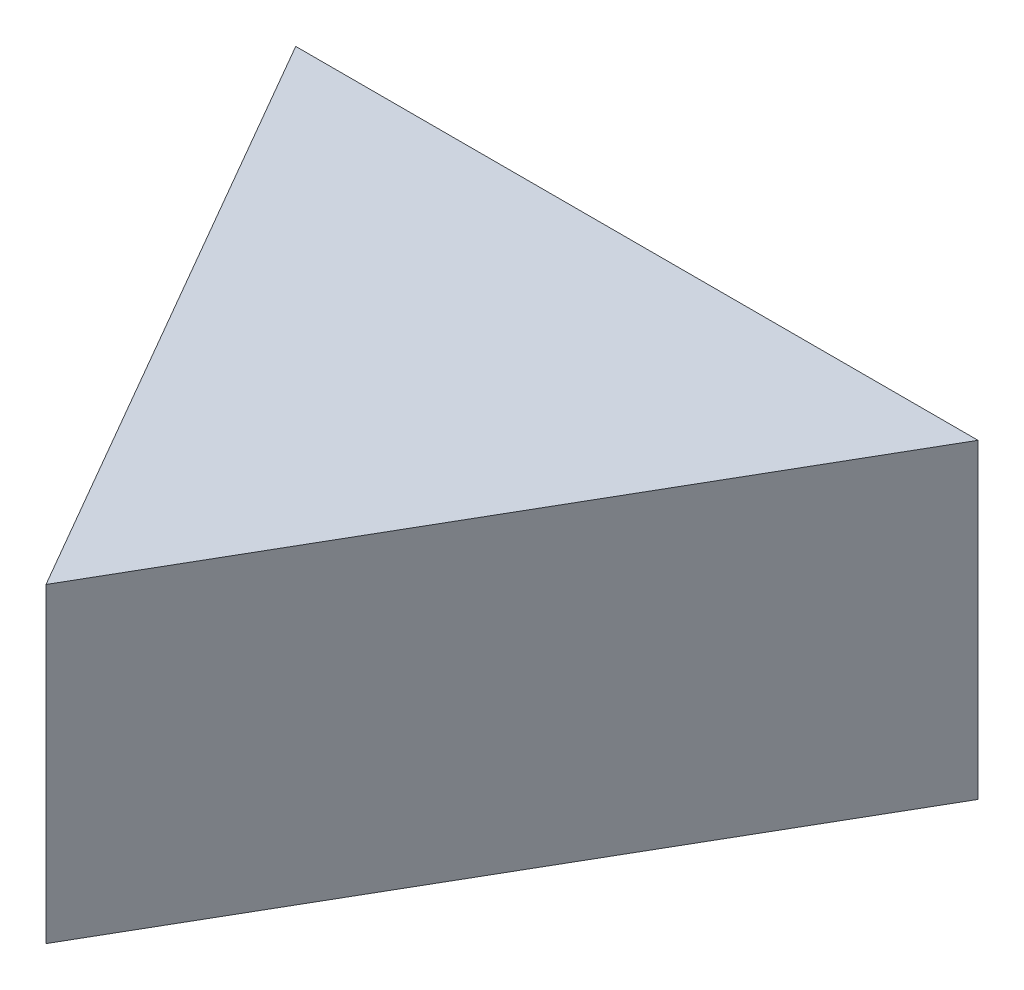
SolidWorks part; units mm, degrees
ref_plane "Front Plane" through (0, 0, 0) normal (0, 0, 1) x (1, 0, 0)
ref_plane "Top Plane" through (0, 0, 0) normal (0, 1, 0) x (1, 0, 0)
ref_plane "Right Plane" through (0, 0, 0) normal (1, 0, 0) x (0, 0, -1)
sketch "Sketch1" plane through (0, 0, 0) normal (0, 1, 0) x (1, 0, 0)
  line L0 (44.45, 0) -> (86.2383, 72.3795)
  line L1 (0, 0) -> (88.9, 0) construction
  line L2 (0, 0) -> (0, 72.3795) construction
  line L3 (0, 72.3795) -> (88.9, 72.3795) construction
  line L4 (88.9, 0) -> (88.9, 72.3795) construction
  line L5 (44.45, 0) -> (2.6617, 72.3795)
  line L6 (44.45, 0) -> (44.45, 72.3795) construction
  line L7 (2.6617, 72.3795) -> (86.2383, 72.3795)
  arc A0 (62.0998, 30.5703) -> (44.45, -35.2995) centre (44.45, 0) ccw construction
  arc A1 (44.45, -35.2995) -> (26.8002, 30.5703) centre (44.45, 0) ccw construction
extrude "Boss-Extrude1" add sketch "Sketch1" along normal blind 38.1
